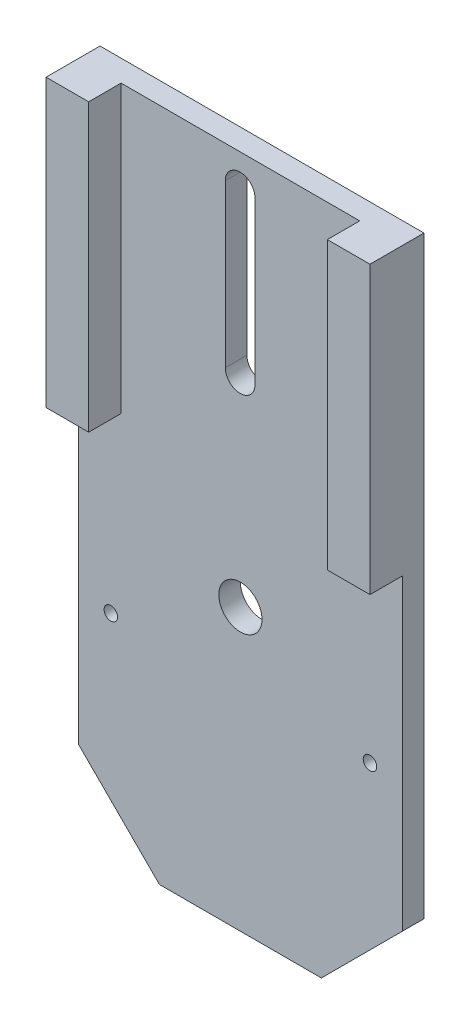
SolidWorks part; units mm, degrees
material "3.1325 (EN-AW 2017A)"
ref_plane "Plan de face" through (0, 0, 0) normal (0, 0, 1) x (1, 0, 0)
ref_plane "Plan de dessus" through (0, 0, 0) normal (0, 1, 0) x (1, 0, 0)
ref_plane "Plan de droite" through (0, 0, 0) normal (1, 0, 0) x (0, 0, -1)
sketch "Esquisse1" plane through (0, 0, 0) normal (0, 0, 1) x (1, 0, 0)
  line L1 (0, 0) -> (60, 0)
  line L2 (0, 0) -> (0, 125)
  line L3 (0, 125) -> (60, 125)
  line L4 (60, 0) -> (60, 125)
  dimension "D1" = 60
  dimension "D2" = 125
extrude "Boss.-Extru.1" add sketch "Esquisse1" along normal blind 10
sketch "Esquisse2" plane through (0, 0, 10) normal (0, 0, 1) x (1, 0, 0)
  line L0 (0, 0) -> (60, 0) construction
  circle A0 centre (30, 52) radius 4
  dimension "D1" = 52
extrude "Enlèv. mat.-Extru.1" cut sketch "Esquisse2" against normal through all
sketch "Esquisse4" plane through (0, 0, 0) normal (-1, 0, 0) x (0, 0, 1)
  line L0 (0, 52) -> (10, 52) construction
  line L1 (10, 0) -> (4, 0)
  line L2 (10, 0) -> (10, 72)
  line L3 (10, 72) -> (4, 72)
  line L4 (4, 0) -> (4, 72)
  dimension "D1" = 20
  dimension "D2" = 6
extrude "Enlèv. mat.-Extru.2" cut sketch "Esquisse4" against normal through all
hole_wizard "Trou taraudé M33" positions "Esquisse10" profile "Esquisse9" tap size "M3" standard "ISO" end condition through all
sketch "Esquisse10" plane through (0, 0, 4) normal (0, 0, 1) x (1, 0, 0)
  circle A0 centre (30, 52) radius 4 construction
  point P0 (54, 39)
  dimension "D1" = 24
  dimension "D2" = 13
sketch "Esquisse9" plane through (54, 39, 4) normal (1, 0, 0) x (0, -1, 0)
  line L0 (0, 0) -> (0, 4)
  line L1 (0, 4) -> (1.25, 4)
  line L2 (1.25, 4) -> (1.25, 0)
  line L5 (1.25, 0) -> (0, 0)
  line L11 (0, -6.35) -> (0, 107.95) construction
  dimension "Diamètre du trou pour taraudage jusqu'au prochain" = 2.5
  dimension "Profondeur du trou pour taraudage jusqu'au prochain" = 4
cosmetic thread "Filetage de perçage3" parameters "D2"=3
hole_wizard "Trou taraudé M34" positions "Esquisse12" profile "Esquisse11" tap size "M3" standard "ISO" end condition through all
sketch "Esquisse12" plane through (0, 0, 4) normal (0, 0, 1) x (1, 0, 0)
  circle A0 centre (30, 52) radius 4 construction
  point P0 (6, 39)
  dimension "D2" = 13
  dimension "D1" = 24
sketch "Esquisse11" plane through (6, 39, 4) normal (1, 0, 0) x (0, -1, 0)
  line L0 (0, 0) -> (0, 4)
  line L1 (0, 4) -> (1.25, 4)
  line L2 (1.25, 4) -> (1.25, 0)
  line L5 (1.25, 0) -> (0, 0)
  line L11 (0, -6.35) -> (0, 107.95) construction
  dimension "Diamètre du trou pour taraudage jusqu'au prochain" = 2.5
  dimension "Profondeur du trou pour taraudage jusqu'au prochain" = 4
cosmetic thread "Filetage de perçage4" parameters "D2"=3
chamfer "Chanfrein1" distance 15 angle 45 2 edges at (0, 0, 2) (60, 0, 2)
sketch "Esquisse15" plane through (0, 125, 0) normal (0, 1, 0) x (1, 0, 0)
  line L0 (60, -10) -> (0, -10) construction
  line L1 (7.9, -10) -> (52.1, -10)
  line L2 (7.9, -10) -> (7.9, -4)
  line L3 (7.9, -4) -> (52.1, -4)
  line L4 (52.1, -10) -> (52.1, -4)
  line L5 (0, -10) -> (0, 0) construction
  dimension "D1" = 44.2
  dimension "D2" = 7.9
  dimension "D3" = 6
extrude "Enlèv. mat.-Extru.4" cut sketch "Esquisse15" against normal blind 55
sketch "Esquisse16" plane through (0, 0, 0) normal (0, 0, -1) x (-1, 0, 0)
  line L0 (-29.9526, 119) -> (-29.9526, 89) construction
  line L1 (-27.2026, 119) -> (-27.2026, 89)
  line L2 (-32.7026, 119) -> (-32.7026, 89)
  line L3 (-60, 125) -> (0, 125) construction
  arc A0 (-27.2026, 119) -> (-32.7026, 119) centre (-29.9526, 119) ccw
  arc A1 (-32.7026, 89) -> (-27.2026, 89) centre (-29.9526, 89) ccw
  point P2 (-29.9526, 104)
  dimension "D1" = 6
extrude "Enlèv. mat.-Extru.5" cut sketch "Esquisse16" against normal through all
